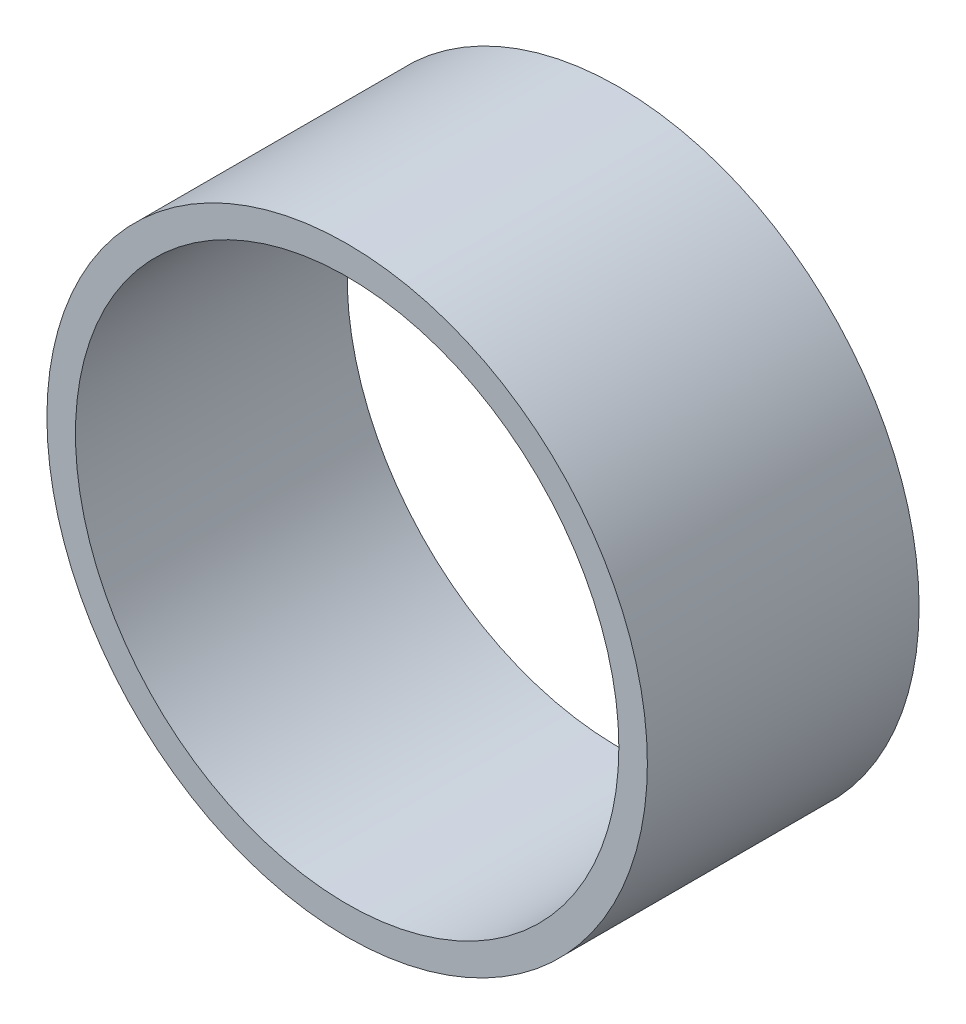
SolidWorks part; units mm, degrees
ref_plane "Front Plane" through (0, 0, 0) normal (0, 0, 1) x (1, 0, 0)
ref_plane "Top Plane" through (0, 0, 0) normal (0, 1, 0) x (1, 0, 0)
ref_plane "Right Plane" through (0, 0, 0) normal (1, 0, 0) x (0, 0, -1)
sketch "Sketch1" plane through (0, 0, 0) normal (0, 0, 1) x (1, 0, 0)
  circle A0 centre (0, 0) radius 4.7625
  circle A1 centre (0, 0) radius 5.2625
  dimension "D1" = 9.525
  dimension "D2" = 10.525
extrude "Boss-Extrude1" add sketch "Sketch1" along normal blind 4.7625
